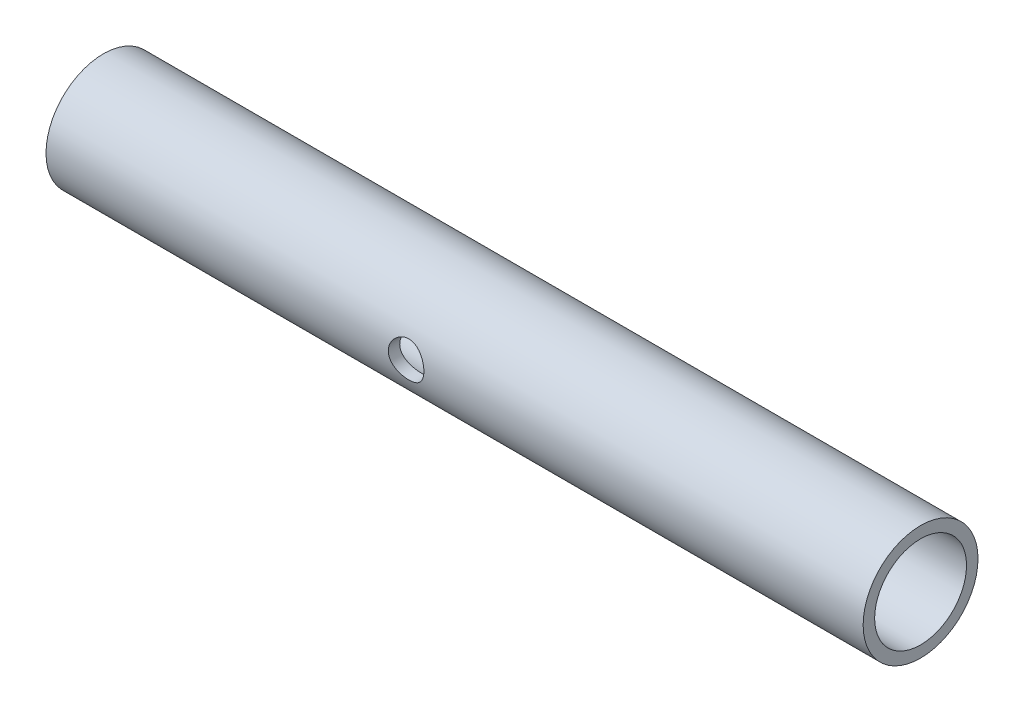
SolidWorks part; units mm, degrees
material "AISI 304"
ref_plane "前视基准面" through (0, 0, 0) normal (0, 0, 1) x (1, 0, 0)
ref_plane "上视基准面" through (0, 0, 0) normal (0, 1, 0) x (1, 0, 0)
ref_plane "右视基准面" through (0, 0, 0) normal (1, 0, 0) x (0, 0, -1)
sketch "草图1" plane through (0, 0, 0) normal (1, 0, 0) x (0, 0, -1)
  circle A0 centre (0, 0) radius 10
  circle A1 centre (0, 0) radius 8
extrude "凸台-拉伸1" add sketch "草图1" along normal blind 107
sketch "草图2" plane through (0, 0, 0) normal (-1, 0, 0) x (0, 0, 1)
  circle A0 centre (0, 0) radius 8
  circle A1 centre (0, 0) radius 10
extrude "凸台-拉伸2" add sketch "草图2" along normal blind 35.3
sketch "草图3" plane through (0, 0, 0) normal (0, 1, 0) x (1, 0, 0)
  line L0 (107, 0) -> (97, 0) construction
  line L1 (107, -10) -> (107, 10) construction
  circle A0 centre (97, 0) radius 3
extrude "切除-拉伸1" [suppressed] cut sketch "草图3" against normal mid plane 30
sketch "草图4" plane through (0, 0, 0) normal (0, 1, 0) x (1, 0, 0)
  line L0 (-35.3, 0) -> (-24, 0) construction
  line L1 (-35.3, 10) -> (-35.3, -10) construction
  circle A0 centre (-24, 0) radius 3.1
extrude "切除-拉伸2" [suppressed] cut sketch "草图4" against normal mid plane 20 contours A0
sketch "Sketch2" plane through (0, 0, 0) normal (0, 0, 1) x (1, 0, 0)
  line L0 (-35.3, 0) -> (27.4, 0) construction
  line L1 (-35.3, 10) -> (-35.3, -10) construction
  circle A0 centre (27.4, 0) radius 3.1
  dimension "D2" = 6.2
  dimension "D1" = 62.7
extrude "Cut-Extrude2" cut sketch "Sketch2" against normal through all and the other way through all
